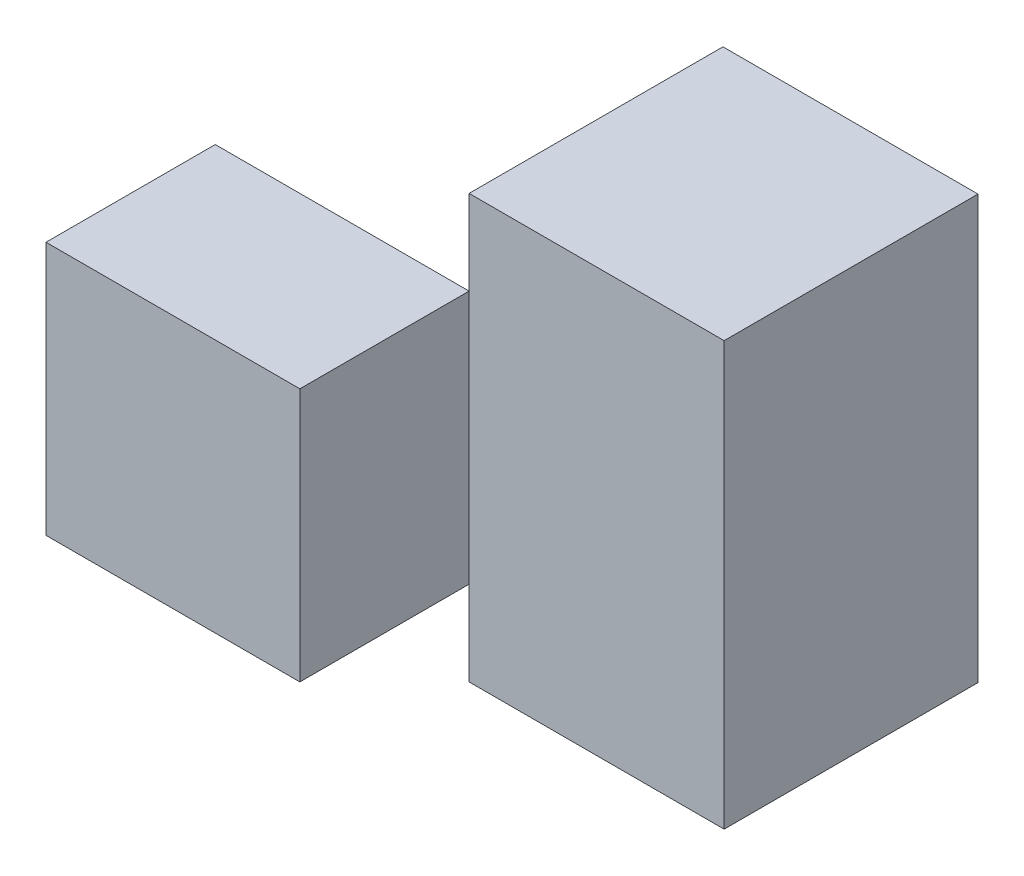
SolidWorks part; units mm, degrees
ref_plane "Front Plane" through (0, 0, 0) normal (0, 0, 1) x (1, 0, 0)
ref_plane "Top Plane" through (0, 0, 0) normal (0, 1, 0) x (1, 0, 0)
ref_plane "Right Plane" through (0, 0, 0) normal (1, 0, 0) x (0, 0, -1)
sketch "Sketch1" plane through (0, 0, 0) normal (0, 0, 1) x (1, 0, 0)
  line L1 (-30, -25) -> (30, -25)
  line L2 (-30, -25) -> (-30, 25)
  line L3 (-30, 25) -> (30, 25)
  line L4 (30, -25) -> (30, 25)
  line L5 (-30, -25) -> (30, 25) construction
  line L6 (-30, 25) -> (30, -25) construction
  point P0 (0, 0)
  dimension "D1" = 60
  dimension "D2" = 50
extrude "Boss-Extrude1" add sketch "Sketch1" along normal blind 50
sketch "Sketch2" plane through (0, 0, 50) normal (0, 0, 1) x (1, 0, 0)
  line L1 (-30, 25) -> (0, 25)
  line L2 (-30, 25) -> (-30, 15)
  line L3 (-30, 15) -> (0, 15)
  line L4 (0, 25) -> (0, 15)
  line L5 (-30, -25) -> (0, -25)
  line L6 (-30, -25) -> (-30, -15)
  line L7 (-30, -15) -> (0, -15)
  line L8 (0, -25) -> (0, -15)
  dimension "D1" = 30
  dimension "D2" = 30
  dimension "D3" = 10
  dimension "D4" = 10
extrude "Cut-Extrude1" cut sketch "Sketch2" against normal blind 50
sketch "Sketch3" plane through (0, 0, 0) normal (-1, 0, 0) x (0, 0, 1)
  line L0 (0, 15) -> (50, 15) construction
  line L1 (50, 25) -> (30, 25)
  line L2 (50, 25) -> (50, 15)
  line L3 (50, 15) -> (30, 15)
  line L4 (30, 25) -> (30, 15)
  line L5 (0, -25) -> (50, -25) construction
  line L6 (50, -15) -> (30, -15)
  line L7 (50, -15) -> (50, -25)
  line L8 (50, -25) -> (30, -25)
  line L9 (30, -15) -> (30, -25)
  dimension "D1" = 20
  dimension "D2" = 20
extrude "Cut-Extrude2" cut sketch "Sketch3" against normal blind 50
sketch "Sketch4" plane through (0, 15, 0) normal (0, 1, 0) x (1, 0, 0)
  line L1 (-30, 0) -> (0, 0)
  line L2 (-30, 0) -> (-30, -30)
  line L3 (-30, -30) -> (0, -30)
  line L4 (0, 0) -> (0, -30)
  line L5 (0, -30) -> (30, -30)
  line L6 (0, -30) -> (0, -50)
  line L7 (0, -50) -> (30, -50)
  line L8 (30, -30) -> (30, -50)
  line M1 (-30, -50) -> (30, -50)
  line M2 (30, -50) -> (30, -30)
  line M3 (30, -30) -> (0, -30)
  line M4 (0, -30) -> (0, 0)
  line M5 (0, 0) -> (-30, 0)
  line M6 (-30, 0) -> (-30, -50)
extrude "Cut-Extrude3" cut sketch "Sketch4" against normal blind 50 contours L3 M6 M4 M5 | L6 M3 M1 M2
ref_plane "Plane2" through (0, 0, 40) normal (0, 0, 1) x (1, 0, 0)
ref_plane "Plane3" through (0, -15, 0) normal (0, 1, 0) x (1, 0, 0)
sketch "Sketch9" plane through (0, -15, 0) normal (0, 1, 0) x (1, 0, 0)
  line L0 (0, 0) -> (29.999, -9.999)
  line L1 (29.999, -9.999) -> (0, -9.999)
  line L2 (0, -9.999) -> (0, 0)
  dimension "D1" = 29.999
  dimension "D2" = 9.999
extrude "Cut-Extrude7" cut sketch "Sketch9" along normal blind 30
sketch "Sketch10" plane through (0, -15, 0) normal (0, 1, 0) x (1, 0, 0)
  line L0 (0, -9.9991) -> (0, -29.9981)
  line L1 (0, -9.9991) -> (29.999, -9.9991)
  line L2 (29.999, -9.9991) -> (0, -29.9981)
  dimension "D1" = 29.999
  dimension "D2" = 19.999
  dimension "D3" = 0.0001
extrude "Cut-Extrude8" cut sketch "Sketch10" along normal blind 30
sketch "Sketch12" plane through (0, 0, 9.999) normal (0, 0, -1) x (-1, 0, 0)
  line L0 (0, -15) -> (0, 15)
  line L1 (0, 15) -> (-29.999, 15)
  line L2 (-29.999, 15) -> (-29.999, -15)
  line L3 (-29.999, -15) -> (0.2652, -15)
  line M1 (-29.999, -15) -> (0, -15)
  line M2 (0, -15) -> (0, 15)
  line M3 (0, 15) -> (-29.999, 15)
  line M4 (-29.999, 15) -> (-29.999, -15)
extrude "Cut-Extrude10" cut sketch "Sketch12" against normal blind 0.0001 contours M4 M1 M2 M3
sketch "Sketch14" plane through (30, 0, 0) normal (1, 0, 0) x (0, 0, -1)
  line L1 (-30, 25) -> (0, 25)
  line L2 (-30, 25) -> (-30, -25)
  line L3 (-30, -25) -> (0, -25)
  line L4 (0, 25) -> (0, -25)
extrude "Boss-Extrude15" add sketch "Sketch14" along normal blind 0.14
